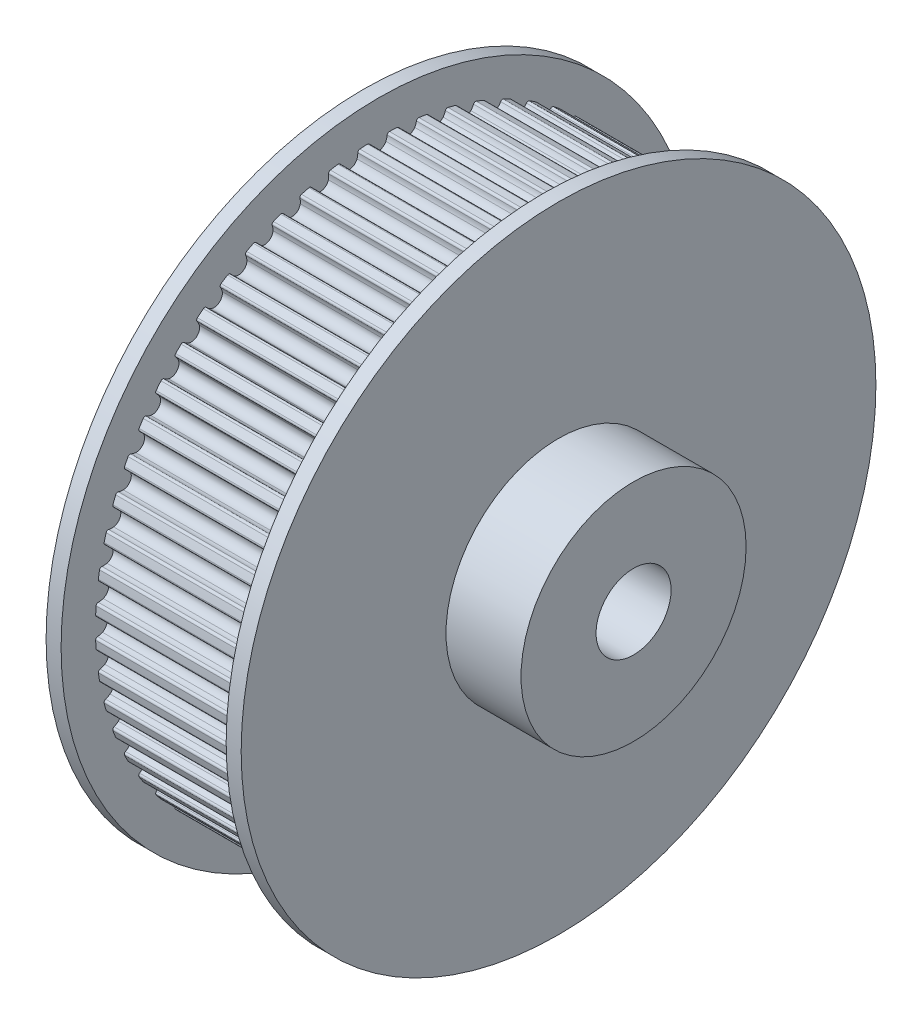
SolidWorks part; units mm, degrees
ref_plane "Front Plane" through (0, 0, 0) normal (0, 0, 1) x (1, 0, 0)
ref_plane "Top Plane" through (0, 0, 0) normal (0, 1, 0) x (1, 0, 0)
ref_plane "Right Plane" through (0, 0, 0) normal (1, 0, 0) x (0, 0, -1)
sketch "Sketch1" plane through (0, 0, 0) normal (1, 0, 0) x (0, 0, -1)
  circle A0 centre (19.0986, 19.0986) radius 5
  arc A1 (37.9444, 18.3683) -> (37.8138, 18.517) centre (37.7944, 18.3683) ccw
  arc A2 (37.49, 18.6022) -> (37.8138, 18.517) centre (37.9027, 19.513) ccw
  arc A3 (37.1832, 19.0986) -> (37.49, 18.6022) centre (37.7382, 19.0986) ccw
  arc A4 (37.49, 19.595) -> (37.1832, 19.0986) centre (37.7382, 19.0986) ccw
  arc A5 (37.8138, 19.6802) -> (37.49, 19.595) centre (37.9027, 18.6842) ccw
  arc A6 (37.8138, 19.6802) -> (37.9444, 19.8289) centre (37.7944, 19.8289) ccw
  arc A7 (37.9444, 19.8289) -> (37.9175, 20.3422) centre (19.114, 19.0994) ccw
  arc A8 (37.9175, 20.3422) -> (37.7721, 20.4765) centre (37.7684, 20.3265) ccw
  arc A9 (37.4411, 20.5273) -> (37.7721, 20.4765) centre (37.7564, 21.4763) ccw
  arc A10 (37.0841, 20.9889) -> (37.4411, 20.5273) centre (37.6361, 21.047) ccw
  arc A11 (37.3373, 21.5147) -> (37.0841, 20.9889) centre (37.6361, 21.047) ccw
  arc A12 (37.6505, 21.6333) -> (37.3373, 21.5147) centre (37.843, 20.652) ccw
  arc A13 (37.6505, 21.6333) -> (37.7649, 21.7949) centre (37.6157, 21.7792) ccw
  arc A14 (37.7649, 21.7949) -> (37.6845, 22.3025) centre (19.1138, 19.101) ccw
  arc A15 (37.6845, 22.3025) -> (37.5258, 22.4208) centre (37.5377, 22.2713) ccw
  arc A16 (37.1913, 22.4368) -> (37.5258, 22.4208) centre (37.4056, 23.4136) ccw
  arc A17 (36.788, 22.8586) -> (37.1913, 22.4368) centre (37.3309, 22.974) ccw
  arc A18 (36.9849, 23.4079) -> (36.788, 22.8586) centre (37.3309, 22.974) ccw
  arc A19 (37.284, 23.5586) -> (36.9849, 23.4079) centre (37.578, 22.6028) ccw
  arc A20 (37.284, 23.5586) -> (37.3808, 23.7312) centre (37.2341, 23.7001) ccw
  arc A21 (37.3808, 23.7312) -> (37.2478, 24.2277) centre (19.1135, 19.1026) ccw
  arc A22 (37.2478, 24.2277) -> (37.0776, 24.3288) centre (37.1051, 24.1813) ccw
  arc A23 (36.7432, 24.3097) -> (37.0776, 24.3288) centre (36.8543, 25.3035) ccw
  arc A24 (36.2981, 24.687) -> (36.7432, 24.3097) centre (36.8259, 24.8585) ccw
  arc A25 (36.4364, 25.254) -> (36.2981, 24.687) centre (36.8259, 24.8585) ccw
  arc A26 (36.7181, 25.4351) -> (36.4364, 25.254) centre (37.1105, 24.5152) ccw
  arc A27 (36.7181, 25.4351) -> (36.7964, 25.6169) centre (36.6537, 25.5705) ccw
  arc A28 (36.7964, 25.6169) -> (36.6122, 26.0967) centre (19.113, 19.1041) ccw
  arc A29 (36.6122, 26.0967) -> (36.4324, 26.1795) centre (36.4752, 26.0357) ccw
  arc A30 (36.1019, 26.1256) -> (36.4324, 26.1795) centre (36.1085, 27.1255) ccw
  arc A31 (35.6197, 26.4543) -> (36.1019, 26.1256) centre (36.1267, 26.68) ccw
  arc A32 (35.6981, 27.0325) -> (35.6197, 26.4543) centre (36.1267, 26.68) ccw
  arc A33 (35.9593, 27.2421) -> (35.6981, 27.0325) centre (36.4456, 26.3683) ccw
  arc A34 (35.9593, 27.2421) -> (36.0181, 27.4311) centre (35.881, 27.3701) ccw
  arc A35 (36.0181, 27.4311) -> (35.7848, 27.889) centre (19.1123, 19.1056) ccw
  arc A36 (35.7848, 27.889) -> (35.5973, 27.9525) centre (35.6548, 27.814) ccw
  arc A37 (35.2742, 27.8644) -> (35.5973, 27.9525) centre (35.1762, 28.8596) ccw
  arc A38 (34.7603, 28.1409) -> (35.2742, 27.8644) centre (35.241, 28.4184) ccw
  arc A39 (34.7778, 28.7242) -> (34.7603, 28.1409) centre (35.241, 28.4184) ccw
  arc A40 (35.0157, 28.9599) -> (34.7778, 28.7242) centre (35.5907, 28.1417) ccw
  arc A41 (35.0157, 28.9599) -> (35.0544, 29.154) centre (34.9245, 29.079) ccw
  arc A42 (35.0544, 29.154) -> (34.7745, 29.585) centre (19.1115, 19.107) ccw
  arc A43 (34.7745, 29.585) -> (34.5814, 29.6286) centre (34.6531, 29.4969) ccw
  arc A44 (34.2693, 29.5072) -> (34.5814, 29.6286) centre (34.0678, 30.4867) ccw
  arc A45 (33.7293, 29.7285) -> (34.2693, 29.5072) centre (34.1783, 30.0547) ccw
  arc A46 (33.6858, 30.3104) -> (33.7293, 29.7285) centre (34.1783, 30.0547) ccw
  arc A47 (33.8977, 30.5697) -> (33.6858, 30.3104) centre (34.5551, 29.8161) ccw
  arc A48 (33.8977, 30.5697) -> (33.9159, 30.7668) centre (33.7946, 30.6786) ccw
  arc A49 (33.9159, 30.7668) -> (33.5925, 31.1662) centre (19.1106, 19.1083) ccw
  arc A50 (33.5925, 31.1662) -> (33.3959, 31.1893) centre (33.481, 31.0658) ccw
  arc A51 (33.0982, 31.0359) -> (33.3959, 31.1893) centre (32.7955, 31.989) ccw
  arc A52 (32.5381, 31.1995) -> (33.0982, 31.0359) centre (32.9505, 31.5709) ccw
  arc A53 (32.4339, 31.7737) -> (32.5381, 31.1995) centre (32.9505, 31.5709) ccw
  arc A54 (32.6176, 32.0538) -> (32.4339, 31.7737) centre (33.3501, 31.373) ccw
  arc A55 (32.6176, 32.0538) -> (32.6151, 32.2517) centre (32.5036, 32.1513) ccw
  arc A56 (32.6151, 32.2517) -> (32.2517, 32.6151) centre (19.1095, 19.1095) ccw
  arc A57 (32.2517, 32.6151) -> (32.0538, 32.6176) centre (32.1513, 32.5036) ccw
  arc A58 (31.7737, 32.4339) -> (32.0538, 32.6176) centre (31.373, 33.3501) ccw
  arc A59 (31.1995, 32.5381) -> (31.7737, 32.4339) centre (31.5709, 32.9505) ccw
  arc A60 (31.0359, 33.0982) -> (31.1995, 32.5381) centre (31.5709, 32.9505) ccw
  arc A61 (31.1893, 33.3959) -> (31.0359, 33.0982) centre (31.989, 32.7955) ccw
  arc A62 (31.1893, 33.3959) -> (31.1662, 33.5925) centre (31.0658, 33.481) ccw
  arc A63 (31.1662, 33.5925) -> (30.7668, 33.9159) centre (19.1083, 19.1106) ccw
  arc A64 (30.7668, 33.9159) -> (30.5697, 33.8977) centre (30.6786, 33.7946) ccw
  arc A65 (30.3104, 33.6858) -> (30.5697, 33.8977) centre (29.8161, 34.5551) ccw
  arc A66 (29.7285, 33.7293) -> (30.3104, 33.6858) centre (30.0547, 34.1783) ccw
  arc A67 (29.5072, 34.2693) -> (29.7285, 33.7293) centre (30.0547, 34.1783) ccw
  arc A68 (29.6286, 34.5814) -> (29.5072, 34.2693) centre (30.4867, 34.0678) ccw
  arc A69 (29.6286, 34.5814) -> (29.585, 34.7745) centre (29.4969, 34.6531) ccw
  arc A70 (29.585, 34.7745) -> (29.154, 35.0544) centre (19.107, 19.1115) ccw
  arc A71 (29.154, 35.0544) -> (28.9599, 35.0157) centre (29.079, 34.9245) ccw
  arc A72 (28.7242, 34.7778) -> (28.9599, 35.0157) centre (28.1417, 35.5907) ccw
  arc A73 (28.1409, 34.7603) -> (28.7242, 34.7778) centre (28.4184, 35.241) ccw
  arc A74 (27.8644, 35.2742) -> (28.1409, 34.7603) centre (28.4184, 35.241) ccw
  arc A75 (27.9525, 35.5973) -> (27.8644, 35.2742) centre (28.8596, 35.1762) ccw
  arc A76 (27.9525, 35.5973) -> (27.889, 35.7848) centre (27.814, 35.6548) ccw
  arc A77 (27.889, 35.7848) -> (27.4311, 36.0181) centre (19.1056, 19.1123) ccw
  arc A78 (27.4311, 36.0181) -> (27.2421, 35.9593) centre (27.3701, 35.881) ccw
  arc A79 (27.0325, 35.6981) -> (27.2421, 35.9593) centre (26.3683, 36.4456) ccw
  arc A80 (26.4543, 35.6197) -> (27.0325, 35.6981) centre (26.68, 36.1267) ccw
  arc A81 (26.1256, 36.1019) -> (26.4543, 35.6197) centre (26.68, 36.1267) ccw
  arc A82 (26.1795, 36.4324) -> (26.1256, 36.1019) centre (27.1255, 36.1085) ccw
  arc A83 (26.1795, 36.4324) -> (26.0967, 36.6122) centre (26.0357, 36.4752) ccw
  arc A84 (26.0967, 36.6122) -> (25.6169, 36.7964) centre (19.1041, 19.113) ccw
  arc A85 (25.6169, 36.7964) -> (25.4351, 36.7181) centre (25.5705, 36.6537) ccw
  arc A86 (25.254, 36.4364) -> (25.4351, 36.7181) centre (24.5152, 37.1105) ccw
  arc A87 (24.687, 36.2981) -> (25.254, 36.4364) centre (24.8585, 36.8259) ccw
  arc A88 (24.3097, 36.7432) -> (24.687, 36.2981) centre (24.8585, 36.8259) ccw
  arc A89 (24.3288, 37.0776) -> (24.3097, 36.7432) centre (25.3035, 36.8543) ccw
  arc A90 (24.3288, 37.0776) -> (24.2277, 37.2478) centre (24.1813, 37.1051) ccw
  arc A91 (24.2277, 37.2478) -> (23.7312, 37.3808) centre (19.1026, 19.1135) ccw
  arc A92 (23.7312, 37.3808) -> (23.5586, 37.284) centre (23.7001, 37.2341) ccw
  arc A93 (23.4079, 36.9849) -> (23.5586, 37.284) centre (22.6028, 37.578) ccw
  arc A94 (22.8586, 36.788) -> (23.4079, 36.9849) centre (22.974, 37.3309) ccw
  arc A95 (22.4368, 37.1913) -> (22.8586, 36.788) centre (22.974, 37.3309) ccw
  arc A96 (22.4208, 37.5258) -> (22.4368, 37.1913) centre (23.4136, 37.4056) ccw
  arc A97 (22.4208, 37.5258) -> (22.3025, 37.6845) centre (22.2713, 37.5377) ccw
  arc A98 (22.3025, 37.6845) -> (21.7949, 37.7649) centre (19.101, 19.1138) ccw
  arc A99 (21.7949, 37.7649) -> (21.6333, 37.6505) centre (21.7792, 37.6157) ccw
  arc A100 (21.5147, 37.3373) -> (21.6333, 37.6505) centre (20.652, 37.843) ccw
  arc A101 (20.9889, 37.0841) -> (21.5147, 37.3373) centre (21.047, 37.6361) ccw
  arc A102 (20.5273, 37.4411) -> (20.9889, 37.0841) centre (21.047, 37.6361) ccw
  arc A103 (20.4765, 37.7721) -> (20.5273, 37.4411) centre (21.4763, 37.7564) ccw
  arc A104 (20.4765, 37.7721) -> (20.3422, 37.9175) centre (20.3265, 37.7684) ccw
  arc A105 (20.3422, 37.9175) -> (19.8289, 37.9444) centre (19.0994, 19.114) ccw
  arc A106 (19.8289, 37.9444) -> (19.6802, 37.8138) centre (19.8289, 37.7944) ccw
  arc A107 (19.595, 37.49) -> (19.6802, 37.8138) centre (18.6842, 37.9027) ccw
  arc A108 (19.0986, 37.1832) -> (19.595, 37.49) centre (19.0986, 37.7382) ccw
  arc A109 (18.6022, 37.49) -> (19.0986, 37.1832) centre (19.0986, 37.7382) ccw
  arc A110 (18.517, 37.8138) -> (18.6022, 37.49) centre (19.513, 37.9027) ccw
  arc A111 (18.517, 37.8138) -> (18.3683, 37.9444) centre (18.3683, 37.7944) ccw
  arc A112 (18.3683, 37.9444) -> (17.855, 37.9175) centre (19.0978, 19.114) ccw
  arc A113 (17.855, 37.9175) -> (17.7207, 37.7721) centre (17.8707, 37.7684) ccw
  arc A114 (17.6699, 37.4411) -> (17.7207, 37.7721) centre (16.7209, 37.7564) ccw
  arc A115 (17.2082, 37.0841) -> (17.6699, 37.4411) centre (17.1502, 37.6361) ccw
  arc A116 (16.6825, 37.3373) -> (17.2082, 37.0841) centre (17.1502, 37.6361) ccw
  arc A117 (16.5639, 37.6505) -> (16.6825, 37.3373) centre (17.5452, 37.843) ccw
  arc A118 (16.5639, 37.6505) -> (16.4023, 37.7649) centre (16.418, 37.6157) ccw
  arc A119 (16.4023, 37.7649) -> (15.8947, 37.6845) centre (19.0962, 19.1138) ccw
  arc A120 (15.8947, 37.6845) -> (15.7764, 37.5258) centre (15.9259, 37.5377) ccw
  arc A121 (15.7604, 37.1913) -> (15.7764, 37.5258) centre (14.7836, 37.4056) ccw
  arc A122 (15.3386, 36.788) -> (15.7604, 37.1913) centre (15.2232, 37.3309) ccw
  arc A123 (14.7892, 36.9849) -> (15.3386, 36.788) centre (15.2232, 37.3309) ccw
  arc A124 (14.6386, 37.284) -> (14.7892, 36.9849) centre (15.5944, 37.578) ccw
  arc A125 (14.6386, 37.284) -> (14.4659, 37.3808) centre (14.4971, 37.2341) ccw
  arc A126 (14.4659, 37.3808) -> (13.9695, 37.2478) centre (19.0946, 19.1135) ccw
  arc A127 (13.9695, 37.2478) -> (13.8684, 37.0776) centre (14.0159, 37.1051) ccw
  arc A128 (13.8875, 36.7432) -> (13.8684, 37.0776) centre (12.8936, 36.8543) ccw
  arc A129 (13.5101, 36.2981) -> (13.8875, 36.7432) centre (13.3386, 36.8259) ccw
  arc A130 (12.9432, 36.4364) -> (13.5101, 36.2981) centre (13.3386, 36.8259) ccw
  arc A131 (12.7621, 36.7181) -> (12.9432, 36.4364) centre (13.682, 37.1105) ccw
  arc A132 (12.7621, 36.7181) -> (12.5803, 36.7964) centre (12.6267, 36.6537) ccw
  arc A133 (12.5803, 36.7964) -> (12.1005, 36.6122) centre (19.0931, 19.113) ccw
  arc A134 (12.1005, 36.6122) -> (12.0177, 36.4324) centre (12.1615, 36.4752) ccw
  arc A135 (12.0716, 36.1019) -> (12.0177, 36.4324) centre (11.0717, 36.1085) ccw
  arc A136 (11.7429, 35.6197) -> (12.0716, 36.1019) centre (11.5172, 36.1267) ccw
  arc A137 (11.1647, 35.6981) -> (11.7429, 35.6197) centre (11.5172, 36.1267) ccw
  arc A138 (10.9551, 35.9593) -> (11.1647, 35.6981) centre (11.8289, 36.4456) ccw
  arc A139 (10.9551, 35.9593) -> (10.7661, 36.0181) centre (10.8271, 35.881) ccw
  arc A140 (10.7661, 36.0181) -> (10.3082, 35.7848) centre (19.0916, 19.1123) ccw
  arc A141 (10.3082, 35.7848) -> (10.2446, 35.5973) centre (10.3832, 35.6548) ccw
  arc A142 (10.3328, 35.2742) -> (10.2446, 35.5973) centre (9.3376, 35.1762) ccw
  arc A143 (10.0563, 34.7603) -> (10.3328, 35.2742) centre (9.7788, 35.241) ccw
  arc A144 (9.473, 34.7778) -> (10.0563, 34.7603) centre (9.7788, 35.241) ccw
  arc A145 (9.2373, 35.0157) -> (9.473, 34.7778) centre (10.0554, 35.5907) ccw
  arc A146 (9.2373, 35.0157) -> (9.0432, 35.0544) centre (9.1182, 34.9245) ccw
  arc A147 (9.0432, 35.0544) -> (8.6121, 34.7745) centre (19.0902, 19.1115) ccw
  arc A148 (8.6121, 34.7745) -> (8.5686, 34.5814) centre (8.7003, 34.6531) ccw
  arc A149 (8.69, 34.2693) -> (8.5686, 34.5814) centre (7.7105, 34.0678) ccw
  arc A150 (8.4687, 33.7293) -> (8.69, 34.2693) centre (8.1425, 34.1783) ccw
  arc A151 (7.8868, 33.6858) -> (8.4687, 33.7293) centre (8.1425, 34.1783) ccw
  arc A152 (7.6275, 33.8977) -> (7.8868, 33.6858) centre (8.3811, 34.5551) ccw
  arc A153 (7.6275, 33.8977) -> (7.4304, 33.9159) centre (7.5186, 33.7946) ccw
  arc A154 (7.4304, 33.9159) -> (7.031, 33.5925) centre (19.0889, 19.1106) ccw
  arc A155 (7.031, 33.5925) -> (7.0079, 33.3959) centre (7.1314, 33.481) ccw
  arc A156 (7.1613, 33.0982) -> (7.0079, 33.3959) centre (6.2082, 32.7955) ccw
  arc A157 (6.9976, 32.5381) -> (7.1613, 33.0982) centre (6.6263, 32.9505) ccw
  arc A158 (6.4234, 32.4339) -> (6.9976, 32.5381) centre (6.6263, 32.9505) ccw
  arc A159 (6.1434, 32.6176) -> (6.4234, 32.4339) centre (6.8242, 33.3501) ccw
  arc A160 (6.1434, 32.6176) -> (5.9455, 32.6151) centre (6.0459, 32.5036) ccw
  arc A161 (5.9455, 32.6151) -> (5.5821, 32.2517) centre (19.0877, 19.1095) ccw
  arc A162 (5.5821, 32.2517) -> (5.5796, 32.0538) centre (5.6936, 32.1513) ccw
  arc A163 (5.7633, 31.7737) -> (5.5796, 32.0538) centre (4.8471, 31.373) ccw
  arc A164 (5.6591, 31.1995) -> (5.7633, 31.7737) centre (5.2467, 31.5709) ccw
  arc A165 (5.099, 31.0359) -> (5.6591, 31.1995) centre (5.2467, 31.5709) ccw
  arc A166 (4.8013, 31.1893) -> (5.099, 31.0359) centre (5.4017, 31.989) ccw
  arc A167 (4.8013, 31.1893) -> (4.6047, 31.1662) centre (4.7162, 31.0658) ccw
  arc A168 (4.6047, 31.1662) -> (4.2813, 30.7668) centre (19.0866, 19.1083) ccw
  arc A169 (4.2813, 30.7668) -> (4.2995, 30.5697) centre (4.4026, 30.6786) ccw
  arc A170 (4.5114, 30.3104) -> (4.2995, 30.5697) centre (3.6421, 29.8161) ccw
  arc A171 (4.4678, 29.7285) -> (4.5114, 30.3104) centre (4.0188, 30.0547) ccw
  arc A172 (3.9279, 29.5072) -> (4.4678, 29.7285) centre (4.0188, 30.0547) ccw
  arc A173 (3.6158, 29.6286) -> (3.9279, 29.5072) centre (4.1293, 30.4867) ccw
  arc A174 (3.6158, 29.6286) -> (3.4227, 29.585) centre (3.544, 29.4969) ccw
  arc A175 (3.4227, 29.585) -> (3.1428, 29.154) centre (19.0857, 19.107) ccw
  arc A176 (3.1428, 29.154) -> (3.1815, 28.9599) centre (3.2727, 29.079) ccw
  arc A177 (3.4194, 28.7242) -> (3.1815, 28.9599) centre (2.6065, 28.1417) ccw
  arc A178 (3.4369, 28.1409) -> (3.4194, 28.7242) centre (2.9562, 28.4184) ccw
  arc A179 (2.923, 27.8644) -> (3.4369, 28.1409) centre (2.9562, 28.4184) ccw
  arc A180 (2.5999, 27.9525) -> (2.923, 27.8644) centre (3.021, 28.8596) ccw
  arc A181 (2.5999, 27.9525) -> (2.4124, 27.889) centre (2.5423, 27.814) ccw
  arc A182 (2.4124, 27.889) -> (2.1791, 27.4311) centre (19.0849, 19.1056) ccw
  arc A183 (2.1791, 27.4311) -> (2.2379, 27.2421) centre (2.3161, 27.3701) ccw
  arc A184 (2.4991, 27.0325) -> (2.2379, 27.2421) centre (1.7516, 26.3683) ccw
  arc A185 (2.5775, 26.4543) -> (2.4991, 27.0325) centre (2.0705, 26.68) ccw
  arc A186 (2.0953, 26.1256) -> (2.5775, 26.4543) centre (2.0705, 26.68) ccw
  arc A187 (1.7648, 26.1795) -> (2.0953, 26.1256) centre (2.0887, 27.1255) ccw
  arc A188 (1.7648, 26.1795) -> (1.585, 26.0967) centre (1.722, 26.0357) ccw
  arc A189 (1.585, 26.0967) -> (1.4008, 25.6169) centre (19.0842, 19.1041) ccw
  arc A190 (1.4008, 25.6169) -> (1.4791, 25.4351) centre (1.5435, 25.5705) ccw
  arc A191 (1.7607, 25.254) -> (1.4791, 25.4351) centre (1.0867, 24.5152) ccw
  arc A192 (1.8991, 24.687) -> (1.7607, 25.254) centre (1.3713, 24.8585) ccw
  arc A193 (1.4539, 24.3097) -> (1.8991, 24.687) centre (1.3713, 24.8585) ccw
  arc A194 (1.1196, 24.3288) -> (1.4539, 24.3097) centre (1.3429, 25.3035) ccw
  arc A195 (1.1196, 24.3288) -> (0.9494, 24.2277) centre (1.0921, 24.1813) ccw
  arc A196 (0.9494, 24.2277) -> (0.8164, 23.7312) centre (19.0837, 19.1026) ccw
  arc A197 (0.8164, 23.7312) -> (0.9132, 23.5586) centre (0.9631, 23.7001) ccw
  arc A198 (1.2123, 23.4079) -> (0.9132, 23.5586) centre (0.6192, 22.6028) ccw
  arc A199 (1.4092, 22.8586) -> (1.2123, 23.4079) centre (0.8663, 22.974) ccw
  arc A200 (1.0059, 22.4368) -> (1.4092, 22.8586) centre (0.8663, 22.974) ccw
  arc A201 (0.6714, 22.4208) -> (1.0059, 22.4368) centre (0.7915, 23.4136) ccw
  arc A202 (0.6714, 22.4208) -> (0.5127, 22.3025) centre (0.6594, 22.2713) ccw
  arc A203 (0.5127, 22.3025) -> (0.4323, 21.7949) centre (19.0834, 19.101) ccw
  arc A204 (0.4323, 21.7949) -> (0.5467, 21.6333) centre (0.5815, 21.7792) ccw
  arc A205 (0.8598, 21.5147) -> (0.5467, 21.6333) centre (0.3542, 20.652) ccw
  arc A206 (1.1131, 20.9889) -> (0.8598, 21.5147) centre (0.5611, 21.047) ccw
  arc A207 (0.7561, 20.5273) -> (1.1131, 20.9889) centre (0.5611, 21.047) ccw
  arc A208 (0.4251, 20.4765) -> (0.7561, 20.5273) centre (0.4408, 21.4763) ccw
  arc A209 (0.4251, 20.4765) -> (0.2796, 20.3422) centre (0.4288, 20.3265) ccw
  arc A210 (0.2796, 20.3422) -> (0.2527, 19.8289) centre (19.0832, 19.0994) ccw
  arc A211 (0.2527, 19.8289) -> (0.3833, 19.6802) centre (0.4027, 19.8289) ccw
  arc A212 (0.7072, 19.595) -> (0.3833, 19.6802) centre (0.2945, 18.6842) ccw
  arc A213 (1.014, 19.0986) -> (0.7072, 19.595) centre (0.459, 19.0986) ccw
  arc A214 (0.7072, 18.6022) -> (1.014, 19.0986) centre (0.459, 19.0986) ccw
  arc A215 (0.3833, 18.517) -> (0.7072, 18.6022) centre (0.2945, 19.513) ccw
  arc A216 (0.3833, 18.517) -> (0.2527, 18.3683) centre (0.4027, 18.3683) ccw
  arc A217 (0.2527, 18.3683) -> (0.2796, 17.855) centre (19.0832, 19.0978) ccw
  arc A218 (0.2796, 17.855) -> (0.4251, 17.7207) centre (0.4288, 17.8707) ccw
  arc A219 (0.7561, 17.6699) -> (0.4251, 17.7207) centre (0.4408, 16.7209) ccw
  arc A220 (1.1131, 17.2082) -> (0.7561, 17.6699) centre (0.5611, 17.1502) ccw
  arc A221 (0.8598, 16.6825) -> (1.1131, 17.2082) centre (0.5611, 17.1502) ccw
  arc A222 (0.5467, 16.5639) -> (0.8598, 16.6825) centre (0.3542, 17.5452) ccw
  arc A223 (0.5467, 16.5639) -> (0.4323, 16.4023) centre (0.5815, 16.418) ccw
  arc A224 (0.4323, 16.4023) -> (0.5127, 15.8947) centre (19.0834, 19.0962) ccw
  arc A225 (0.5127, 15.8947) -> (0.6714, 15.7764) centre (0.6594, 15.9259) ccw
  arc A226 (1.0059, 15.7604) -> (0.6714, 15.7764) centre (0.7915, 14.7836) ccw
  arc A227 (1.4092, 15.3386) -> (1.0059, 15.7604) centre (0.8663, 15.2232) ccw
  arc A228 (1.2123, 14.7892) -> (1.4092, 15.3386) centre (0.8663, 15.2232) ccw
  arc A229 (0.9132, 14.6386) -> (1.2123, 14.7892) centre (0.6192, 15.5944) ccw
  arc A230 (0.9132, 14.6386) -> (0.8164, 14.4659) centre (0.9631, 14.4971) ccw
  arc A231 (0.8164, 14.4659) -> (0.9494, 13.9695) centre (19.0837, 19.0946) ccw
  arc A232 (0.9494, 13.9695) -> (1.1196, 13.8684) centre (1.0921, 14.0159) ccw
  arc A233 (1.4539, 13.8875) -> (1.1196, 13.8684) centre (1.3429, 12.8936) ccw
  arc A234 (1.8991, 13.5101) -> (1.4539, 13.8875) centre (1.3713, 13.3386) ccw
  arc A235 (1.7607, 12.9432) -> (1.8991, 13.5101) centre (1.3713, 13.3386) ccw
  arc A236 (1.4791, 12.7621) -> (1.7607, 12.9432) centre (1.0867, 13.682) ccw
  arc A237 (1.4791, 12.7621) -> (1.4008, 12.5803) centre (1.5435, 12.6267) ccw
  arc A238 (1.4008, 12.5803) -> (1.585, 12.1005) centre (19.0842, 19.0931) ccw
  arc A239 (1.585, 12.1005) -> (1.7648, 12.0177) centre (1.722, 12.1615) ccw
  arc A240 (2.0953, 12.0716) -> (1.7648, 12.0177) centre (2.0887, 11.0717) ccw
  arc A241 (2.5775, 11.7429) -> (2.0953, 12.0716) centre (2.0705, 11.5172) ccw
  arc A242 (2.4991, 11.1647) -> (2.5775, 11.7429) centre (2.0705, 11.5172) ccw
  arc A243 (2.2379, 10.9551) -> (2.4991, 11.1647) centre (1.7516, 11.8289) ccw
  arc A244 (2.2379, 10.9551) -> (2.1791, 10.7661) centre (2.3161, 10.8271) ccw
  arc A245 (2.1791, 10.7661) -> (2.4124, 10.3082) centre (19.0849, 19.0916) ccw
  arc A246 (2.4124, 10.3082) -> (2.5999, 10.2446) centre (2.5423, 10.3832) ccw
  arc A247 (2.923, 10.3328) -> (2.5999, 10.2446) centre (3.021, 9.3376) ccw
  arc A248 (3.4369, 10.0563) -> (2.923, 10.3328) centre (2.9562, 9.7788) ccw
  arc A249 (3.4194, 9.473) -> (3.4369, 10.0563) centre (2.9562, 9.7788) ccw
  arc A250 (3.1815, 9.2373) -> (3.4194, 9.473) centre (2.6065, 10.0554) ccw
  arc A251 (3.1815, 9.2373) -> (3.1428, 9.0432) centre (3.2727, 9.1182) ccw
  arc A252 (3.1428, 9.0432) -> (3.4227, 8.6121) centre (19.0857, 19.0902) ccw
  arc A253 (3.4227, 8.6121) -> (3.6158, 8.5686) centre (3.544, 8.7003) ccw
  arc A254 (3.9279, 8.69) -> (3.6158, 8.5686) centre (4.1293, 7.7105) ccw
  arc A255 (4.4678, 8.4687) -> (3.9279, 8.69) centre (4.0188, 8.1425) ccw
  arc A256 (4.5114, 7.8868) -> (4.4678, 8.4687) centre (4.0188, 8.1425) ccw
  arc A257 (4.2995, 7.6275) -> (4.5114, 7.8868) centre (3.6421, 8.3811) ccw
  arc A258 (4.2995, 7.6275) -> (4.2813, 7.4304) centre (4.4026, 7.5186) ccw
  arc A259 (4.2813, 7.4304) -> (4.6047, 7.031) centre (19.0866, 19.0889) ccw
  arc A260 (4.6047, 7.031) -> (4.8013, 7.0079) centre (4.7162, 7.1314) ccw
  arc A261 (5.099, 7.1613) -> (4.8013, 7.0079) centre (5.4017, 6.2082) ccw
  arc A262 (5.6591, 6.9976) -> (5.099, 7.1613) centre (5.2467, 6.6263) ccw
  arc A263 (5.7633, 6.4234) -> (5.6591, 6.9976) centre (5.2467, 6.6263) ccw
  arc A264 (5.5796, 6.1434) -> (5.7633, 6.4234) centre (4.8471, 6.8242) ccw
  arc A265 (5.5796, 6.1434) -> (5.5821, 5.9455) centre (5.6936, 6.0459) ccw
  arc A266 (5.5821, 5.9455) -> (5.9455, 5.5821) centre (19.0877, 19.0877) ccw
  arc A267 (5.9455, 5.5821) -> (6.1434, 5.5796) centre (6.0459, 5.6936) ccw
  arc A268 (6.4234, 5.7633) -> (6.1434, 5.5796) centre (6.8242, 4.8471) ccw
  arc A269 (6.9976, 5.6591) -> (6.4234, 5.7633) centre (6.6263, 5.2467) ccw
  arc A270 (7.1613, 5.099) -> (6.9976, 5.6591) centre (6.6263, 5.2467) ccw
  arc A271 (7.0079, 4.8013) -> (7.1613, 5.099) centre (6.2082, 5.4017) ccw
  arc A272 (7.0079, 4.8013) -> (7.031, 4.6047) centre (7.1314, 4.7162) ccw
  arc A273 (7.031, 4.6047) -> (7.4304, 4.2813) centre (19.0889, 19.0866) ccw
  arc A274 (7.4304, 4.2813) -> (7.6275, 4.2995) centre (7.5186, 4.4026) ccw
  arc A275 (7.8868, 4.5114) -> (7.6275, 4.2995) centre (8.3811, 3.6421) ccw
  arc A276 (8.4687, 4.4678) -> (7.8868, 4.5114) centre (8.1425, 4.0188) ccw
  arc A277 (8.69, 3.9279) -> (8.4687, 4.4678) centre (8.1425, 4.0188) ccw
  arc A278 (8.5686, 3.6158) -> (8.69, 3.9279) centre (7.7105, 4.1293) ccw
  arc A279 (8.5686, 3.6158) -> (8.6121, 3.4227) centre (8.7003, 3.544) ccw
  arc A280 (8.6121, 3.4227) -> (9.0432, 3.1428) centre (19.0902, 19.0857) ccw
  arc A281 (9.0432, 3.1428) -> (9.2373, 3.1815) centre (9.1182, 3.2727) ccw
  arc A282 (9.473, 3.4194) -> (9.2373, 3.1815) centre (10.0554, 2.6065) ccw
  arc A283 (10.0563, 3.4369) -> (9.473, 3.4194) centre (9.7788, 2.9562) ccw
  arc A284 (10.3328, 2.923) -> (10.0563, 3.4369) centre (9.7788, 2.9562) ccw
  arc A285 (10.2446, 2.5999) -> (10.3328, 2.923) centre (9.3376, 3.021) ccw
  arc A286 (10.2446, 2.5999) -> (10.3082, 2.4124) centre (10.3832, 2.5423) ccw
  arc A287 (10.3082, 2.4124) -> (10.7661, 2.1791) centre (19.0916, 19.0849) ccw
  arc A288 (10.7661, 2.1791) -> (10.9551, 2.2379) centre (10.8271, 2.3161) ccw
  arc A289 (11.1647, 2.4991) -> (10.9551, 2.2379) centre (11.8289, 1.7516) ccw
  arc A290 (11.7429, 2.5775) -> (11.1647, 2.4991) centre (11.5172, 2.0705) ccw
  arc A291 (12.0716, 2.0953) -> (11.7429, 2.5775) centre (11.5172, 2.0705) ccw
  arc A292 (12.0177, 1.7648) -> (12.0716, 2.0953) centre (11.0717, 2.0887) ccw
  arc A293 (12.0177, 1.7648) -> (12.1005, 1.585) centre (12.1615, 1.722) ccw
  arc A294 (12.1005, 1.585) -> (12.5803, 1.4008) centre (19.0931, 19.0842) ccw
  arc A295 (12.5803, 1.4008) -> (12.7621, 1.4791) centre (12.6267, 1.5435) ccw
  arc A296 (12.9432, 1.7607) -> (12.7621, 1.4791) centre (13.682, 1.0867) ccw
  arc A297 (13.5101, 1.8991) -> (12.9432, 1.7607) centre (13.3386, 1.3713) ccw
  arc A298 (13.8875, 1.4539) -> (13.5101, 1.8991) centre (13.3386, 1.3713) ccw
  arc A299 (13.8684, 1.1196) -> (13.8875, 1.4539) centre (12.8936, 1.3429) ccw
  arc A300 (13.8684, 1.1196) -> (13.9695, 0.9494) centre (14.0159, 1.0921) ccw
  arc A301 (13.9695, 0.9494) -> (14.4659, 0.8164) centre (19.0946, 19.0837) ccw
  arc A302 (14.4659, 0.8164) -> (14.6386, 0.9132) centre (14.4971, 0.9631) ccw
  arc A303 (14.7892, 1.2123) -> (14.6386, 0.9132) centre (15.5944, 0.6192) ccw
  arc A304 (15.3386, 1.4092) -> (14.7892, 1.2123) centre (15.2232, 0.8663) ccw
  arc A305 (15.7604, 1.0059) -> (15.3386, 1.4092) centre (15.2232, 0.8663) ccw
  arc A306 (15.7764, 0.6714) -> (15.7604, 1.0059) centre (14.7836, 0.7915) ccw
  arc A307 (15.7764, 0.6714) -> (15.8947, 0.5127) centre (15.9259, 0.6594) ccw
  arc A308 (15.8947, 0.5127) -> (16.4023, 0.4323) centre (19.0962, 19.0834) ccw
  arc A309 (16.4023, 0.4323) -> (16.5639, 0.5467) centre (16.418, 0.5815) ccw
  arc A310 (16.6825, 0.8598) -> (16.5639, 0.5467) centre (17.5452, 0.3542) ccw
  arc A311 (17.2082, 1.1131) -> (16.6825, 0.8598) centre (17.1502, 0.5611) ccw
  arc A312 (17.6699, 0.7561) -> (17.2082, 1.1131) centre (17.1502, 0.5611) ccw
  arc A313 (17.7207, 0.4251) -> (17.6699, 0.7561) centre (16.7209, 0.4408) ccw
  arc A314 (17.7207, 0.4251) -> (17.855, 0.2796) centre (17.8707, 0.4288) ccw
  arc A315 (17.855, 0.2796) -> (18.3683, 0.2527) centre (19.0978, 19.0832) ccw
  arc A316 (18.3683, 0.2527) -> (18.517, 0.3833) centre (18.3683, 0.4027) ccw
  arc A317 (18.6022, 0.7072) -> (18.517, 0.3833) centre (19.513, 0.2945) ccw
  arc A318 (19.0986, 1.014) -> (18.6022, 0.7072) centre (19.0986, 0.459) ccw
  arc A319 (19.595, 0.7072) -> (19.0986, 1.014) centre (19.0986, 0.459) ccw
  arc A320 (19.6802, 0.3833) -> (19.595, 0.7072) centre (18.6842, 0.2945) ccw
  arc A321 (19.6802, 0.3833) -> (19.8289, 0.2527) centre (19.8289, 0.4027) ccw
  arc A322 (19.8289, 0.2527) -> (20.3422, 0.2796) centre (19.0994, 19.0832) ccw
  arc A323 (20.3422, 0.2796) -> (20.4765, 0.4251) centre (20.3265, 0.4288) ccw
  arc A324 (20.5273, 0.7561) -> (20.4765, 0.4251) centre (21.4763, 0.4408) ccw
  arc A325 (20.9889, 1.1131) -> (20.5273, 0.7561) centre (21.047, 0.5611) ccw
  arc A326 (21.5147, 0.8598) -> (20.9889, 1.1131) centre (21.047, 0.5611) ccw
  arc A327 (21.6333, 0.5467) -> (21.5147, 0.8598) centre (20.652, 0.3542) ccw
  arc A328 (21.6333, 0.5467) -> (21.7949, 0.4323) centre (21.7792, 0.5815) ccw
  arc A329 (21.7949, 0.4323) -> (22.3025, 0.5127) centre (19.101, 19.0834) ccw
  arc A330 (22.3025, 0.5127) -> (22.4208, 0.6714) centre (22.2713, 0.6594) ccw
  arc A331 (22.4368, 1.0059) -> (22.4208, 0.6714) centre (23.4136, 0.7915) ccw
  arc A332 (22.8586, 1.4092) -> (22.4368, 1.0059) centre (22.974, 0.8663) ccw
  arc A333 (23.4079, 1.2123) -> (22.8586, 1.4092) centre (22.974, 0.8663) ccw
  arc A334 (23.5586, 0.9132) -> (23.4079, 1.2123) centre (22.6028, 0.6192) ccw
  arc A335 (23.5586, 0.9132) -> (23.7312, 0.8164) centre (23.7001, 0.9631) ccw
  arc A336 (23.7312, 0.8164) -> (24.2277, 0.9494) centre (19.1026, 19.0837) ccw
  arc A337 (24.2277, 0.9494) -> (24.3288, 1.1196) centre (24.1813, 1.0921) ccw
  arc A338 (24.3097, 1.4539) -> (24.3288, 1.1196) centre (25.3035, 1.3429) ccw
  arc A339 (24.687, 1.8991) -> (24.3097, 1.4539) centre (24.8585, 1.3713) ccw
  arc A340 (25.254, 1.7607) -> (24.687, 1.8991) centre (24.8585, 1.3713) ccw
  arc A341 (25.4351, 1.4791) -> (25.254, 1.7607) centre (24.5152, 1.0867) ccw
  arc A342 (25.4351, 1.4791) -> (25.6169, 1.4008) centre (25.5705, 1.5435) ccw
  arc A343 (25.6169, 1.4008) -> (26.0967, 1.585) centre (19.1041, 19.0842) ccw
  arc A344 (26.0967, 1.585) -> (26.1795, 1.7648) centre (26.0357, 1.722) ccw
  arc A345 (26.1256, 2.0953) -> (26.1795, 1.7648) centre (27.1255, 2.0887) ccw
  arc A346 (26.4543, 2.5775) -> (26.1256, 2.0953) centre (26.68, 2.0705) ccw
  arc A347 (27.0325, 2.4991) -> (26.4543, 2.5775) centre (26.68, 2.0705) ccw
  arc A348 (27.2421, 2.2379) -> (27.0325, 2.4991) centre (26.3683, 1.7516) ccw
  arc A349 (27.2421, 2.2379) -> (27.4311, 2.1791) centre (27.3701, 2.3161) ccw
  arc A350 (27.4311, 2.1791) -> (27.889, 2.4124) centre (19.1056, 19.0849) ccw
  arc A351 (27.889, 2.4124) -> (27.9525, 2.5999) centre (27.814, 2.5423) ccw
  arc A352 (27.8644, 2.923) -> (27.9525, 2.5999) centre (28.8596, 3.021) ccw
  arc A353 (28.1409, 3.4369) -> (27.8644, 2.923) centre (28.4184, 2.9562) ccw
  arc A354 (28.7242, 3.4194) -> (28.1409, 3.4369) centre (28.4184, 2.9562) ccw
  arc A355 (28.9599, 3.1815) -> (28.7242, 3.4194) centre (28.1417, 2.6065) ccw
  arc A356 (28.9599, 3.1815) -> (29.154, 3.1428) centre (29.079, 3.2727) ccw
  arc A357 (29.154, 3.1428) -> (29.585, 3.4227) centre (19.107, 19.0857) ccw
  arc A358 (29.585, 3.4227) -> (29.6286, 3.6158) centre (29.4969, 3.544) ccw
  arc A359 (29.5072, 3.9279) -> (29.6286, 3.6158) centre (30.4867, 4.1293) ccw
  arc A360 (29.7285, 4.4678) -> (29.5072, 3.9279) centre (30.0547, 4.0188) ccw
  arc A361 (30.3104, 4.5114) -> (29.7285, 4.4678) centre (30.0547, 4.0188) ccw
  arc A362 (30.5697, 4.2995) -> (30.3104, 4.5114) centre (29.8161, 3.6421) ccw
  arc A363 (30.5697, 4.2995) -> (30.7668, 4.2813) centre (30.6786, 4.4026) ccw
  arc A364 (30.7668, 4.2813) -> (31.1662, 4.6047) centre (19.1083, 19.0866) ccw
  arc A365 (31.1662, 4.6047) -> (31.1893, 4.8013) centre (31.0658, 4.7162) ccw
  arc A366 (31.0359, 5.099) -> (31.1893, 4.8013) centre (31.989, 5.4017) ccw
  arc A367 (31.1995, 5.6591) -> (31.0359, 5.099) centre (31.5709, 5.2467) ccw
  arc A368 (31.7737, 5.7633) -> (31.1995, 5.6591) centre (31.5709, 5.2467) ccw
  arc A369 (32.0538, 5.5796) -> (31.7737, 5.7633) centre (31.373, 4.8471) ccw
  arc A370 (32.0538, 5.5796) -> (32.2517, 5.5821) centre (32.1513, 5.6936) ccw
  arc A371 (32.2517, 5.5821) -> (32.6151, 5.9455) centre (19.1095, 19.0877) ccw
  arc A372 (32.6151, 5.9455) -> (32.6176, 6.1434) centre (32.5036, 6.0459) ccw
  arc A373 (32.4339, 6.4234) -> (32.6176, 6.1434) centre (33.3501, 6.8242) ccw
  arc A374 (32.5381, 6.9976) -> (32.4339, 6.4234) centre (32.9505, 6.6263) ccw
  arc A375 (33.0982, 7.1613) -> (32.5381, 6.9976) centre (32.9505, 6.6263) ccw
  arc A376 (33.3959, 7.0079) -> (33.0982, 7.1613) centre (32.7955, 6.2082) ccw
  arc A377 (33.3959, 7.0079) -> (33.5925, 7.031) centre (33.481, 7.1314) ccw
  arc A378 (33.5925, 7.031) -> (33.9159, 7.4304) centre (19.1106, 19.0889) ccw
  arc A379 (33.9159, 7.4304) -> (33.8977, 7.6275) centre (33.7946, 7.5186) ccw
  arc A380 (33.6858, 7.8868) -> (33.8977, 7.6275) centre (34.5551, 8.3811) ccw
  arc A381 (33.7293, 8.4687) -> (33.6858, 7.8868) centre (34.1783, 8.1425) ccw
  arc A382 (34.2693, 8.69) -> (33.7293, 8.4687) centre (34.1783, 8.1425) ccw
  arc A383 (34.5814, 8.5686) -> (34.2693, 8.69) centre (34.0678, 7.7105) ccw
  arc A384 (34.5814, 8.5686) -> (34.7745, 8.6121) centre (34.6531, 8.7003) ccw
  arc A385 (34.7745, 8.6121) -> (35.0544, 9.0432) centre (19.1115, 19.0902) ccw
  arc A386 (35.0544, 9.0432) -> (35.0157, 9.2373) centre (34.9245, 9.1182) ccw
  arc A387 (34.7778, 9.473) -> (35.0157, 9.2373) centre (35.5907, 10.0554) ccw
  arc A388 (34.7603, 10.0563) -> (34.7778, 9.473) centre (35.241, 9.7788) ccw
  arc A389 (35.2742, 10.3328) -> (34.7603, 10.0563) centre (35.241, 9.7788) ccw
  arc A390 (35.5973, 10.2446) -> (35.2742, 10.3328) centre (35.1762, 9.3376) ccw
  arc A391 (35.5973, 10.2446) -> (35.7848, 10.3082) centre (35.6548, 10.3832) ccw
  arc A392 (35.7848, 10.3082) -> (36.0181, 10.7661) centre (19.1123, 19.0916) ccw
  arc A393 (36.0181, 10.7661) -> (35.9593, 10.9551) centre (35.881, 10.8271) ccw
  arc A394 (35.6981, 11.1647) -> (35.9593, 10.9551) centre (36.4456, 11.8289) ccw
  arc A395 (35.6197, 11.7429) -> (35.6981, 11.1647) centre (36.1267, 11.5172) ccw
  arc A396 (36.1019, 12.0716) -> (35.6197, 11.7429) centre (36.1267, 11.5172) ccw
  arc A397 (36.4324, 12.0177) -> (36.1019, 12.0716) centre (36.1085, 11.0717) ccw
  arc A398 (36.4324, 12.0177) -> (36.6122, 12.1005) centre (36.4752, 12.1615) ccw
  arc A399 (36.6122, 12.1005) -> (36.7964, 12.5803) centre (19.113, 19.0931) ccw
  arc A400 (36.7964, 12.5803) -> (36.7181, 12.7621) centre (36.6537, 12.6267) ccw
  arc A401 (36.4364, 12.9432) -> (36.7181, 12.7621) centre (37.1105, 13.682) ccw
  arc A402 (36.2981, 13.5101) -> (36.4364, 12.9432) centre (36.8259, 13.3386) ccw
  arc A403 (36.7432, 13.8875) -> (36.2981, 13.5101) centre (36.8259, 13.3386) ccw
  arc A404 (37.0776, 13.8684) -> (36.7432, 13.8875) centre (36.8543, 12.8936) ccw
  arc A405 (37.0776, 13.8684) -> (37.2478, 13.9695) centre (37.1051, 14.0159) ccw
  arc A406 (37.2478, 13.9695) -> (37.3808, 14.4659) centre (19.1135, 19.0946) ccw
  arc A407 (37.3808, 14.4659) -> (37.284, 14.6386) centre (37.2341, 14.4971) ccw
  arc A408 (36.9849, 14.7892) -> (37.284, 14.6386) centre (37.578, 15.5944) ccw
  arc A409 (36.788, 15.3386) -> (36.9849, 14.7892) centre (37.3309, 15.2232) ccw
  arc A410 (37.1913, 15.7604) -> (36.788, 15.3386) centre (37.3309, 15.2232) ccw
  arc A411 (37.5258, 15.7764) -> (37.1913, 15.7604) centre (37.4056, 14.7836) ccw
  arc A412 (37.5258, 15.7764) -> (37.6845, 15.8947) centre (37.5377, 15.9259) ccw
  arc A413 (37.6845, 15.8947) -> (37.7649, 16.4023) centre (19.1138, 19.0962) ccw
  arc A414 (37.7649, 16.4023) -> (37.6505, 16.5639) centre (37.6157, 16.418) ccw
  arc A415 (37.3373, 16.6825) -> (37.6505, 16.5639) centre (37.843, 17.5452) ccw
  arc A416 (37.0841, 17.2082) -> (37.3373, 16.6825) centre (37.6361, 17.1502) ccw
  arc A417 (37.4411, 17.6699) -> (37.0841, 17.2082) centre (37.6361, 17.1502) ccw
  arc A418 (37.7721, 17.7207) -> (37.4411, 17.6699) centre (37.7564, 16.7209) ccw
  arc A419 (37.7721, 17.7207) -> (37.9175, 17.855) centre (37.7684, 17.8707) ccw
  arc A420 (37.9175, 17.855) -> (37.9444, 18.3683) centre (19.114, 19.0978) ccw
extrude "Boss-Extrude1" add sketch "Sketch1" along normal blind 11
sketch "Sketch2" plane through (11, 0, 0) normal (1, 0, 0) x (0, 0, -1)
  circle A0 centre (19.0986, 19.0986) radius 5 construction
  circle A1 centre (19.0986, 19.0986) radius 5
  circle A2 centre (19.0986, 19.0986) radius 2.5
  dimension "D1" = 10
  dimension "D2" = 5
extrude "Boss-Extrude2" add sketch "Sketch2" against normal up to surface (11 mm away) up to face at (0, 19.0986, -19.0986)
sketch "Sketch3" plane through (0, 0, 0) normal (-1, 0, 0) x (0, 0, 1)
  circle A0 centre (-19.0986, 19.0986) radius 21.15
  circle A1 centre (-19.0986, 19.0986) radius 2.5 construction
  circle A2 centre (-19.0986, 19.0986) radius 2.5
  dimension "D1" = 42.3
extrude "Boss-Extrude3" add sketch "Sketch3" along normal blind 1
sketch "Sketch4" plane through (11, 0, 0) normal (1, 0, 0) x (0, 0, -1)
  circle A1 centre (19.0986, 19.0986) radius 2.5
  circle A2 centre (19.0986, 19.0986) radius 2.5
  circle A3 centre (19.0986, 19.0986) radius 21.15
  circle A4 centre (19.0986, 19.0986) radius 21.15
  dimension "D1" = 0
  dimension "D2" = 0
extrude "Boss-Extrude4" add sketch "Sketch4" along normal blind 1
sketch "Sketch5" plane through (12, 0, 0) normal (1, 0, 0) x (0, 0, -1)
  circle A0 centre (19.0986, 19.0986) radius 7.5
  circle A1 centre (19.0986, 19.0986) radius 2.5 construction
  circle A2 centre (19.0986, 19.0986) radius 2.5
  dimension "D1" = 15
extrude "Boss-Extrude5" add sketch "Sketch5" along normal blind 5
